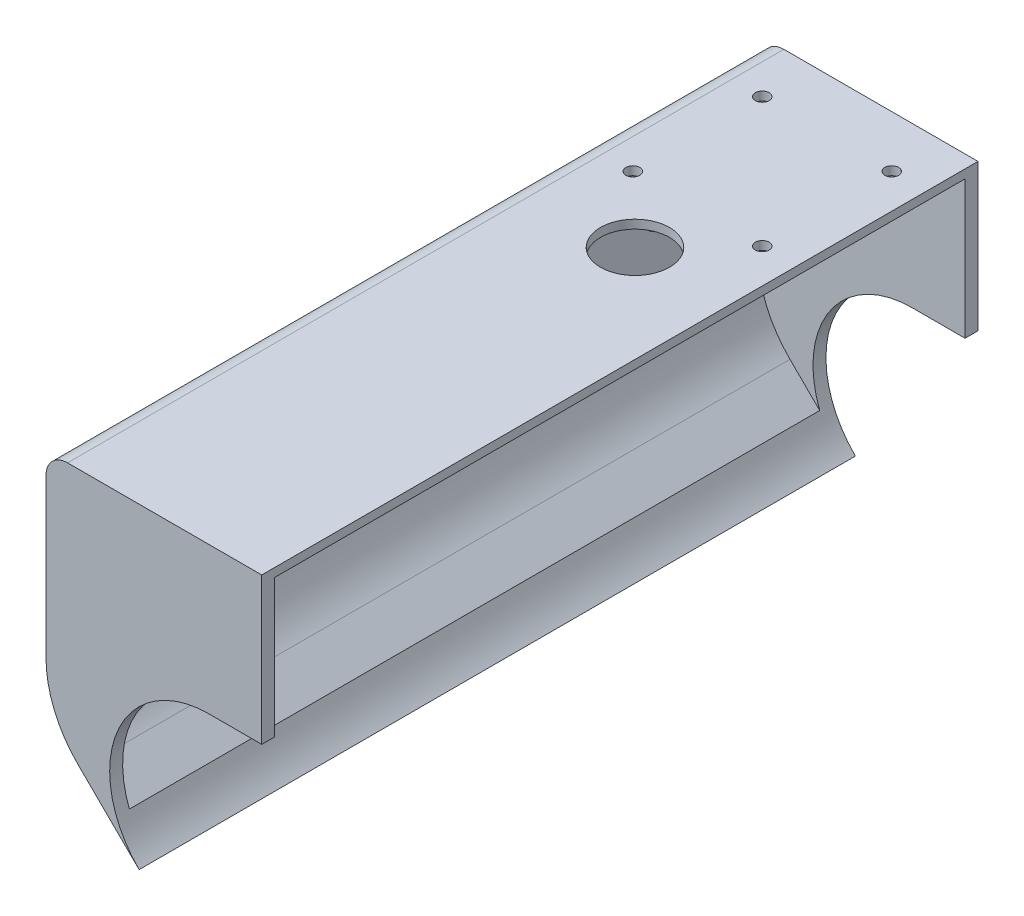
SolidWorks part; units mm, degrees
ref_plane "Front Plane" through (0, 0, 0) normal (0, 0, 1) x (1, 0, 0)
ref_plane "Top Plane" through (0, 0, 0) normal (0, 1, 0) x (1, 0, 0)
ref_plane "Right Plane" through (0, 0, 0) normal (1, 0, 0) x (0, 0, -1)
sketch "Sketch1" plane through (0, 0, 0) normal (0, 0, 1) x (1, 0, 0)
  line L0 (-176.4226, 3.6462) -> (-198.0073, 24.9918)
  line L1 (-198.0073, 24.9918) -> (-198.0073, 77)
  line L2 (-198.0073, 77) -> (-148.0073, 77)
  line L4 (-160.25, 43) -> (-148.0073, 43)
  line L6 (-148.0073, 43) -> (-148.0073, 77)
  arc A1 (-160.25, 43) -> (-176.4226, 3.6462) centre (-160.25, 20) ccw
extrude "Boss-Extrude1" add sketch "Sketch1" against normal blind 3
sketch "Sketch2" plane through (0, 0, -166) normal (0, 0, -1) x (-1, 0, 0)
  line L5 (198.0073, 24.9918) -> (198.0073, 77)
  line L6 (198.0073, 77) -> (148.0073, 77)
  line L7 (148.0073, 77) -> (148.0073, 43)
  line L8 (148.0073, 43) -> (160.25, 43)
  line L9 (176.4226, 3.6462) -> (198.0073, 24.9918)
  line L10 (198.0073, 24.9918) -> (198.0073, 77)
  line L11 (198.0073, 77) -> (148.0073, 77)
  line L12 (148.0073, 77) -> (148.0073, 43)
  line L13 (148.0073, 43) -> (160.25, 43)
  line L14 (176.4226, 3.6462) -> (198.0073, 24.9918)
  arc A1 (176.4226, 3.6462) -> (160.25, 43) centre (160.25, 20) ccw
  arc A2 (176.4226, 3.6462) -> (160.25, 43) centre (160.25, 20) ccw
  dimension "D1" = 0
extrude "Boss-Extrude2" add sketch "Sketch2" against normal blind 3 separate body
sketch "Sketch3" plane through (0, 0, -3) normal (0, 0, -1) x (-1, 0, 0)
  line L0 (181.6864, 11.6645) -> (196.0073, 25.8268)
  line L1 (196.0073, 25.8268) -> (196.0073, 75)
  line L2 (196.0073, 75) -> (148.0073, 75)
  line L3 (148.0073, 77) -> (148.0073, 75)
  line L4 (175.0163, 5.0683) -> (196.0073, 25.8268) construction
  line L5 (198.0073, 24.9918) -> (198.0073, 77)
  line L6 (198.0073, 77) -> (148.0073, 77)
  line L7 (148.0073, 77) -> (148.0073, 43)
  line L8 (148.0073, 43) -> (160.25, 43)
  line L9 (176.4226, 3.6462) -> (198.0073, 24.9918)
  line L10 (198.0073, 24.9918) -> (198.0073, 77)
  line L11 (198.0073, 77) -> (148.0073, 77)
  line L14 (176.4226, 3.6462) -> (198.0073, 24.9918)
  arc A0 (160.25, -3) -> (160.25, 43) centre (160.25, 20) ccw construction
  arc A1 (176.4226, 3.6462) -> (160.25, 43) centre (160.25, 20) ccw
  arc A3 (176.4226, 3.6462) -> (181.6864, 11.6645) centre (160.25, 20) ccw
  dimension "D1" = 0
  dimension "D2" = 2
extrude "Boss-Extrude3" add sketch "Sketch3" along normal up to surface (160 mm away) up to face at (-173.6482, 45.6762, -163)
fillet "Fillet1" radius 5 2 edges at (-198.0073, 77, -83) (-196.0073, 75, -83)
fillet "Fillet2" radius 25 2 edges at (-196.0073, 25.8268, -83) (-198.0073, 24.9918, -83)
sketch "Sketch4" plane through (-198.0073, 0, 0) normal (-1, 0, 0) x (0, 0, 1)
  line L0 (-83, 77) -> (-83, 3.6462) construction
  line L1 (-166, 77) -> (0, 77) construction
  line L2 (-166, 3.6462) -> (0, 3.6462) construction
  line L3 (-112, 59.5) -> (-54, 59.5)
  line L4 (-112, 67) -> (-54, 67)
  line L5 (-113, 66) -> (-113, 65)
  line L6 (-112, 64) -> (-54, 64)
  line L7 (-53, 66) -> (-53, 65)
  line L8 (-113, 58.5) -> (-113, 57.5)
  line L9 (-112, 56.5) -> (-54, 56.5)
  line L10 (-53, 58.5) -> (-53, 57.5)
  line L11 (-112, 52) -> (-54, 52)
  line L12 (-113, 51) -> (-113, 50)
  line L13 (-112, 49) -> (-54, 49)
  line L14 (-53, 51) -> (-53, 50)
  line L15 (-112, 44.5) -> (-54, 44.5)
  line L16 (-113, 43.5) -> (-113, 42.5)
  line L17 (-112, 41.5) -> (-54, 41.5)
  line L18 (-53, 43.5) -> (-53, 42.5)
  arc A0 (-54, 67) -> (-53, 66) centre (-54, 66) cw
  arc A1 (-54, 64) -> (-53, 65) centre (-54, 65) ccw
  arc A2 (-112, 67) -> (-113, 66) centre (-112, 66) ccw
  arc A3 (-113, 65) -> (-112, 64) centre (-112, 65) ccw
  arc A4 (-54, 59.5) -> (-53, 58.5) centre (-54, 58.5) cw
  arc A5 (-54, 56.5) -> (-53, 57.5) centre (-54, 57.5) ccw
  arc A6 (-112, 59.5) -> (-113, 58.5) centre (-112, 58.5) ccw
  arc A7 (-113, 57.5) -> (-112, 56.5) centre (-112, 57.5) ccw
  arc A8 (-54, 52) -> (-53, 51) centre (-54, 51) cw
  arc A9 (-54, 49) -> (-53, 50) centre (-54, 50) ccw
  arc A10 (-112, 52) -> (-113, 51) centre (-112, 51) ccw
  arc A11 (-113, 50) -> (-112, 49) centre (-112, 50) ccw
  arc A12 (-54, 44.5) -> (-53, 43.5) centre (-54, 43.5) cw
  arc A13 (-54, 41.5) -> (-53, 42.5) centre (-54, 42.5) ccw
  arc A14 (-112, 44.5) -> (-113, 43.5) centre (-112, 43.5) ccw
  arc A15 (-113, 42.5) -> (-112, 41.5) centre (-112, 42.5) ccw
  dimension "D1" = 1
  dimension "D2" = 4
extrude "Cut-Extrude1" cut sketch "Sketch4" against normal blind 5
sketch "Sketch5" plane through (0, 77, 0) normal (0, 1, 0) x (1, 0, 0)
  circle A0 centre (-170.5073, 109) radius 8
extrude "Cut-Extrude2" cut sketch "Sketch5" against normal blind 2
sketch "Sketch6" plane through (0, 77, 0) normal (0, 1, 0) x (1, 0, 0)
  circle A0 centre (-156.0073, 154) radius 1.6
  circle A1 centre (-156.0073, 124) radius 1.6
  circle A2 centre (-186.0073, 124) radius 1.6
  circle A3 centre (-186.0073, 154) radius 1.6
extrude "Cut-Extrude3" cut sketch "Sketch6" against normal up to surface (2 mm away) up to face at (-170.5073, 75, -101)
sketch "Sketch7" plane through (-198.0073, 0, 0) normal (-1, 0, 0) x (0, 0, 1)
  circle A0 centre (-141, 57) radius 5
extrude "Cut-Extrude4" cut sketch "Sketch7" against normal blind 3
